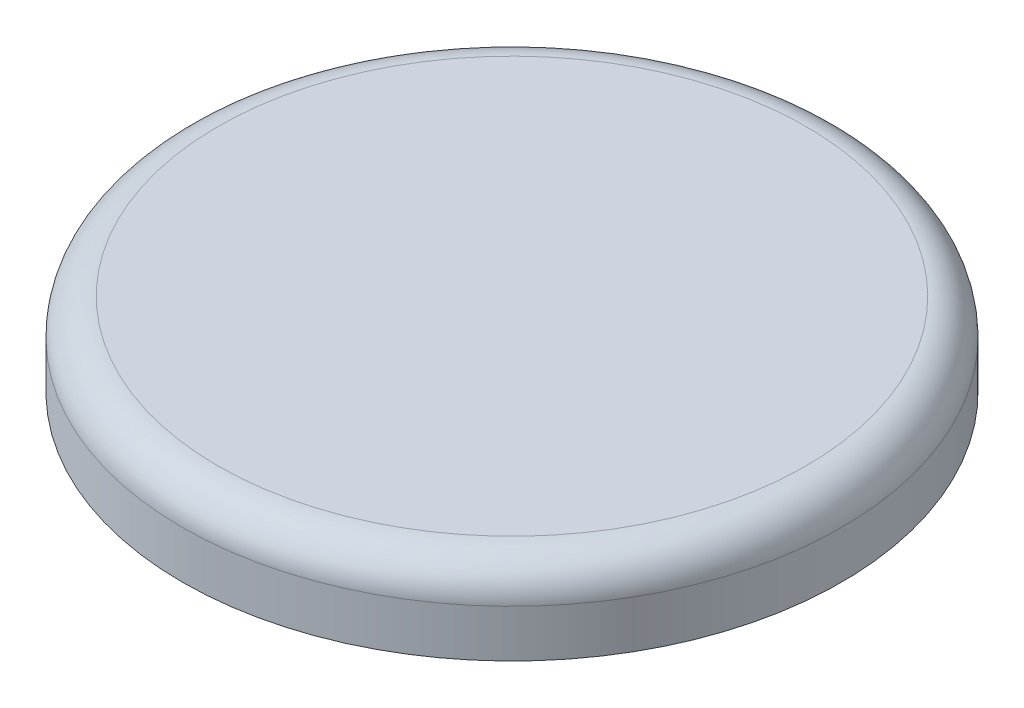
SolidWorks part; units mm, degrees
ref_plane "Front Plane" through (0, 0, 0) normal (0, 0, 1) x (1, 0, 0)
ref_plane "Top Plane" through (0, 0, 0) normal (0, 1, 0) x (1, 0, 0)
ref_plane "Right Plane" through (0, 0, 0) normal (1, 0, 0) x (0, 0, -1)
sketch "Sketch1" plane through (0, 0, 0) normal (0, 1, 0) x (1, 0, 0)
  circle A0 centre (0, 0) radius 27.81
  dimension "D1" = 55.62
extrude "Boss-Extrude1" add sketch "Sketch1" along normal blind 7 contours A0
fillet "Fillet1" radius 3 1 edges at (0, 7, 27.81)
shell "Shell6" thickness 2
sketch "Sketch4" plane through (0, 0, 0) normal (0, 0, 1) x (1, 0, 0)
  line L0 (0, 7.3799) -> (0, 0)
  line L1 (3.65, 7) -> (3.65, 3.6)
  line L2 (4.6, 3.6) -> (3.65, 3.6)
  line L3 (2.5, 0) -> (1.5, 0)
  line L4 (4.6, 3.6) -> (2.5, 0)
  line L5 (1.5, 0) -> (1.5, 7)
  line L6 (1.5, 7) -> (3.65, 7)
  line L7 (24.81, 7) -> (-24.81, 7) construction
  dimension "D1" = 3.65
  dimension "D2" = 3.4
  dimension "D3" = 4.6
  dimension "D4" = 2.5
  dimension "D5" = 1
revolve "Revolve1" add sketch "Sketch4" angle 360 about L0
sketch "Sketch6" plane through (0, 5, 0) normal (0, -1, 0) x (1, 0, 0)
  circle A0 centre (9.8172, 0) radius 2.5
  circle A1 centre (-9.82, 0) radius 2.5
  circle A3 centre (0, 0) radius 4.6 construction
  dimension "D1" = 9.8172
  dimension "D2" = 9.82
  dimension "D3" = 5
  dimension "D4" = 5
extrude "Boss-Extrude5" add sketch "Sketch6" along normal blind 7
move or copy body "Body-Move/Copy1" bodies to move or copy 103 copy no translate (0, -2, 0)
sketch "Sketch9" plane through (0, -2, 0) normal (0, -1, 0) x (1, 0, 0)
  line L0 (0, 0) -> (-12.32, 0) construction
  line L1 (-6.16, 0) -> (-9.82, 0)
  line L3 (-10.57, 4.9125) -> (-9.07, 4.9125)
  line L4 (-10.57, 4.9125) -> (-10.57, -4.9125)
  line L5 (-10.57, -4.9125) -> (-9.07, -4.9125)
  line L6 (-9.07, 4.9125) -> (-9.07, -4.9125)
  line L7 (-10.57, 4.9125) -> (-9.07, -4.9125) construction
  line L8 (-10.57, -4.9125) -> (-9.07, 4.9125) construction
  circle A0 centre (-9.82, 0) radius 2.5 construction
  circle A1 centre (-9.82, 0) radius 1.75
  dimension "D3" = 3.5
  dimension "D1" = 1.5
  dimension "D2" = 9.825
extrude "Cut-Extrude1" cut sketch "Sketch9" against normal up to surface (7 mm away)
sketch "Sketch10" plane through (0, -2, 0) normal (0, -1, 0) x (1, 0, 0)
  line L1 (10.5672, -4.5713) -> (9.0672, -4.5713)
  line L2 (10.5672, -4.5713) -> (10.5672, 4.5713)
  line L3 (10.5672, 4.5713) -> (9.0672, 4.5713)
  line L4 (9.0672, -4.5713) -> (9.0672, 4.5713)
  line L5 (10.5672, -4.5713) -> (9.0672, 4.5713) construction
  line L6 (10.5672, 4.5713) -> (9.0672, -4.5713) construction
  circle A0 centre (9.8172, 0) radius 1.75
  point P0 (9.8172, 0)
  circle M2 centre (9.8172, 0) radius 2.5
  dimension "D2" = 3.5
  dimension "D1" = 1.5
extrude "Cut-Extrude2" cut sketch "Sketch10" against normal up to surface (7 mm away) contours L4 L2 L3 M2 | A0 L2 L4 M2 | L2 A0 L4 | A0 L4 L2 M2 | L4 L1 L2 M2 | L2 A0 | L4 A0 up to face at (-8.3825, 5, 0)
sketch "Sketch12" plane through (0, -2, 0) normal (0, -1, 0) x (1, 0, 0)
  line L1 (-0.75, -6.7057) -> (0.75, -6.7057)
  line L2 (-0.75, -6.7057) -> (-0.75, 6.7057)
  line L3 (-0.75, 6.7057) -> (0.75, 6.7057)
  line L4 (0.75, -6.7057) -> (0.75, 6.7057)
  line L5 (-0.75, -6.7057) -> (0.75, 6.7057) construction
  line L6 (-0.75, 6.7057) -> (0.75, -6.7057) construction
  line L7 (-5.9237, 0.75) -> (5.9237, 0.75)
  line L8 (-5.9237, 0.75) -> (-5.9237, -0.75)
  line L9 (-5.9237, -0.75) -> (5.9237, -0.75)
  line L10 (5.9237, 0.75) -> (5.9237, -0.75)
  line L11 (-5.9237, 0.75) -> (5.9237, -0.75) construction
  line L12 (-5.9237, -0.75) -> (5.9237, 0.75) construction
  circle A0 centre (0, 0) radius 1.75
  point P0 (0, 0)
  circle M3 centre (0, 0) radius 1.5
  circle M4 centre (0, 0) radius 2.5
  dimension "D2" = 3.5
  dimension "D1" = 1.5
  dimension "D3" = 13.4114
  dimension "D4" = 1.5
extrude "Cut-Extrude3" cut sketch "Sketch12" against normal up to surface (7 mm away) contours L4 L3 L2 M4 | A0 L4 L2 M4 | A0 L2 L4 M4 | L1 L4 L2 M4 | L2 A0 M3 | L4 A0 L2 M3 | L4 A0 M3 | L2 A0 L4 M3 | L8 L9 L7 M4 | A0 L7 L9 M4 | L10 L7 L9 M4 | A0 L9 L7 M4
